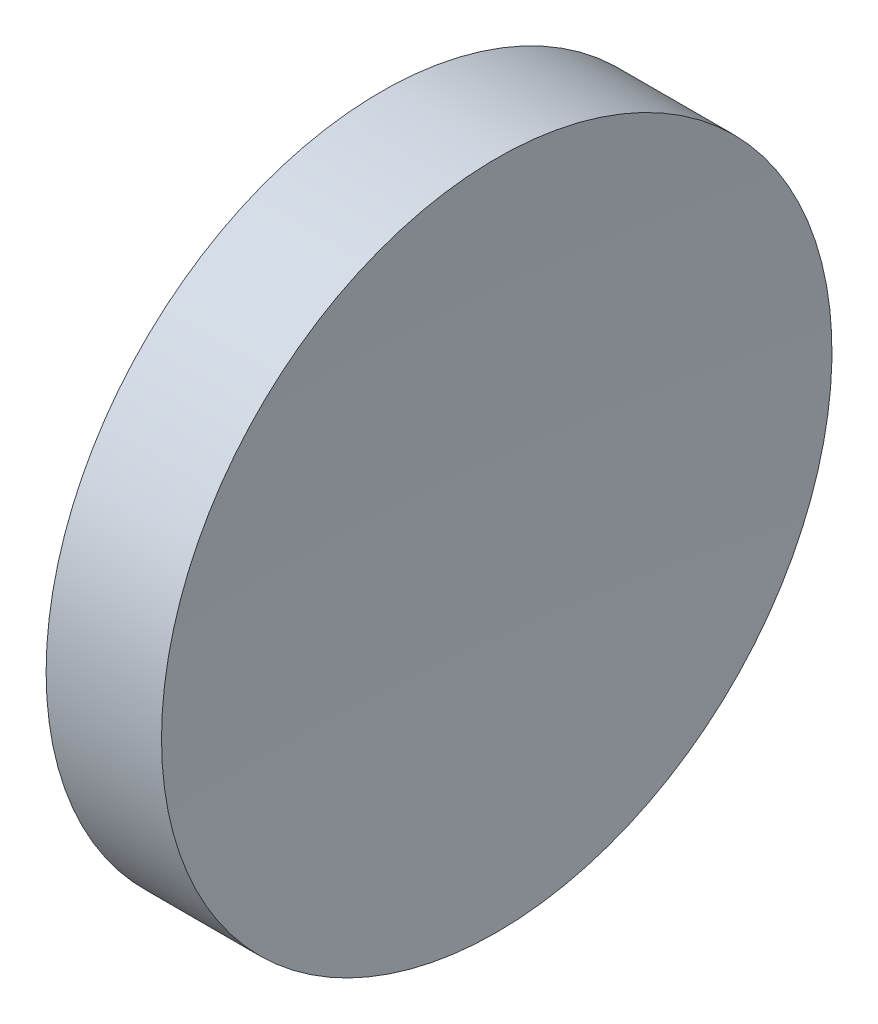
SolidWorks part; units mm, degrees
ref_plane "前视基准面" through (0, 0, 0) normal (0, 0, 1) x (1, 0, 0)
ref_plane "上视基准面" through (0, 0, 0) normal (0, 1, 0) x (1, 0, 0)
ref_plane "右视基准面" through (0, 0, 0) normal (1, 0, 0) x (0, 0, -1)
sketch "草图1" plane through (0, 0, 0) normal (0, 0, 1) x (1, 0, 0)
  line L0 (111.9552, 71.194) -> (137.836, 71.194) construction
  line L1 (119.5068, 71.194) -> (119.5068, 83.894)
  line L2 (119.5068, 83.894) -> (123.879, 83.894)
  line L3 (123.5068, 71.194) -> (119.5068, 71.194)
  arc A0 (123.879, 83.894) -> (123.5068, 71.194) centre (340.4068, 71.194) ccw
revolve "旋转1" add sketch "草图1" angle 360 about L0
